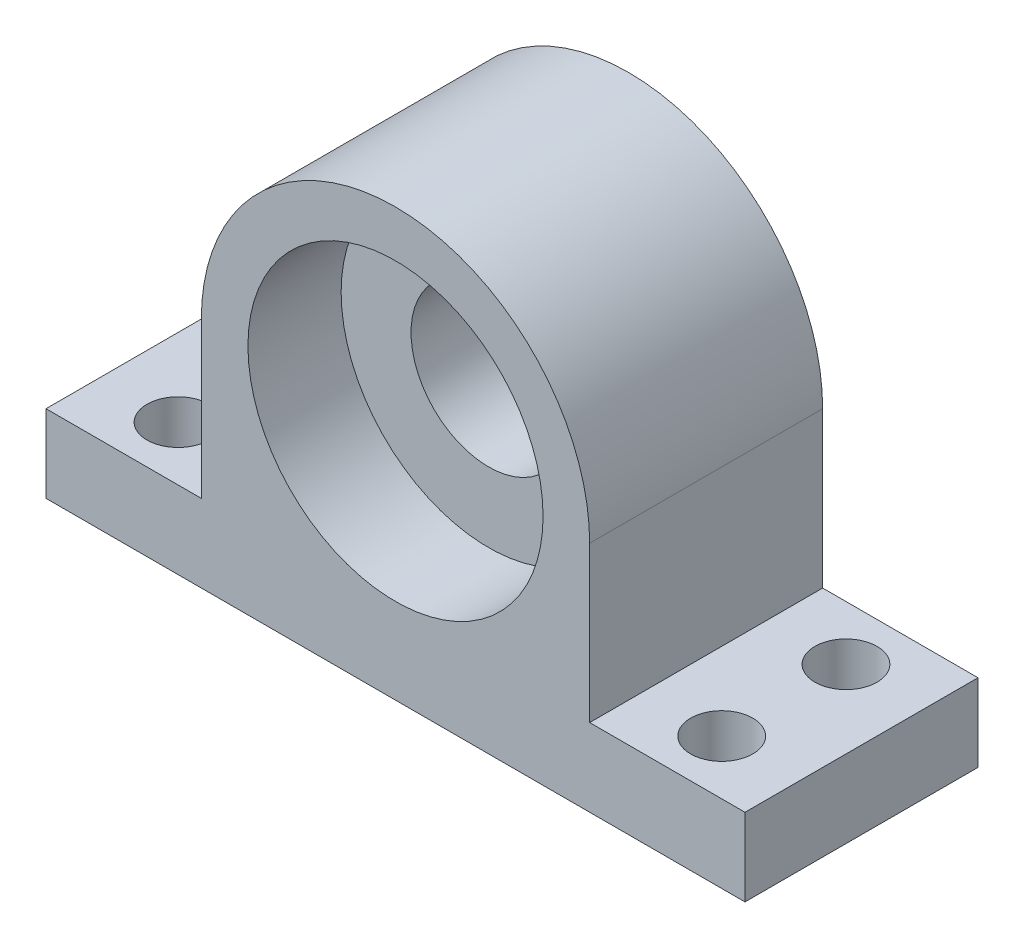
SolidWorks part; units mm, degrees
material "PET"
ref_plane "Front Plane" through (0, 0, 0) normal (0, 0, 1) x (1, 0, 0)
ref_plane "Top Plane" through (0, 0, 0) normal (0, 1, 0) x (1, 0, 0)
ref_plane "Right Plane" through (0, 0, 0) normal (1, 0, 0) x (0, 0, -1)
sketch "Sketch1" plane through (0, 0, 0) normal (0, 0, 1) x (1, 0, 0)
  line L0 (-12.5, 0) -> (-12.5, -10)
  line L1 (-22.5, -10) -> (-12.5, -10)
  line L2 (-22.5, -10) -> (-22.5, -15)
  line L3 (-22.5, -15) -> (22.5, -15)
  line L4 (22.5, -10) -> (22.5, -15)
  line L5 (12.5, 0) -> (12.5, -10)
  line L6 (12.5, -10) -> (22.5, -10)
  arc A0 (12.5, 0) -> (-12.5, 0) centre (0, 0) ccw
  circle A1 centre (0, 0) radius 5
  dimension "D1" = 15
  dimension "D2" = 25
  dimension "D5" = 22.5
  dimension "D6" = 10
  dimension "D3" = 45
  dimension "D4" = 5
extrude "Boss-Extrude1" add sketch "Sketch1" along normal blind 15
sketch "Sketch2" plane through (0, 0, 15) normal (0, 0, 1) x (1, 0, 0)
  circle A0 centre (0, 0) radius 9.5
  dimension "D1" = 19
extrude "Cut-Extrude1" cut sketch "Sketch2" against normal blind 6
sketch "Sketch3" plane through (0, -10, 0) normal (0, 1, 0) x (1, 0, 0)
  line L0 (22.5, -15) -> (22.5, 0) construction
  line L1 (22.5, 0) -> (12.5, 0) construction
  line L2 (22.5, -15) -> (12.5, -15) construction
  line L3 (0, -15) -> (0, -21.1956) construction
  line L4 (-12.5, -15) -> (12.5, -15) construction
  circle A2 centre (17.5, -3.5) radius 2
  circle A3 centre (17.5, -11.5) radius 2
  circle A4 centre (-17.5, -11.5) radius 2
  circle A5 centre (-17.5, -3.5) radius 2
  dimension "D1" = 4
  dimension "D2" = 5
  dimension "D4" = 3.5
  dimension "D3" = 3.5
extrude "Cut-Extrude2" cut sketch "Sketch3" against normal blind 6
